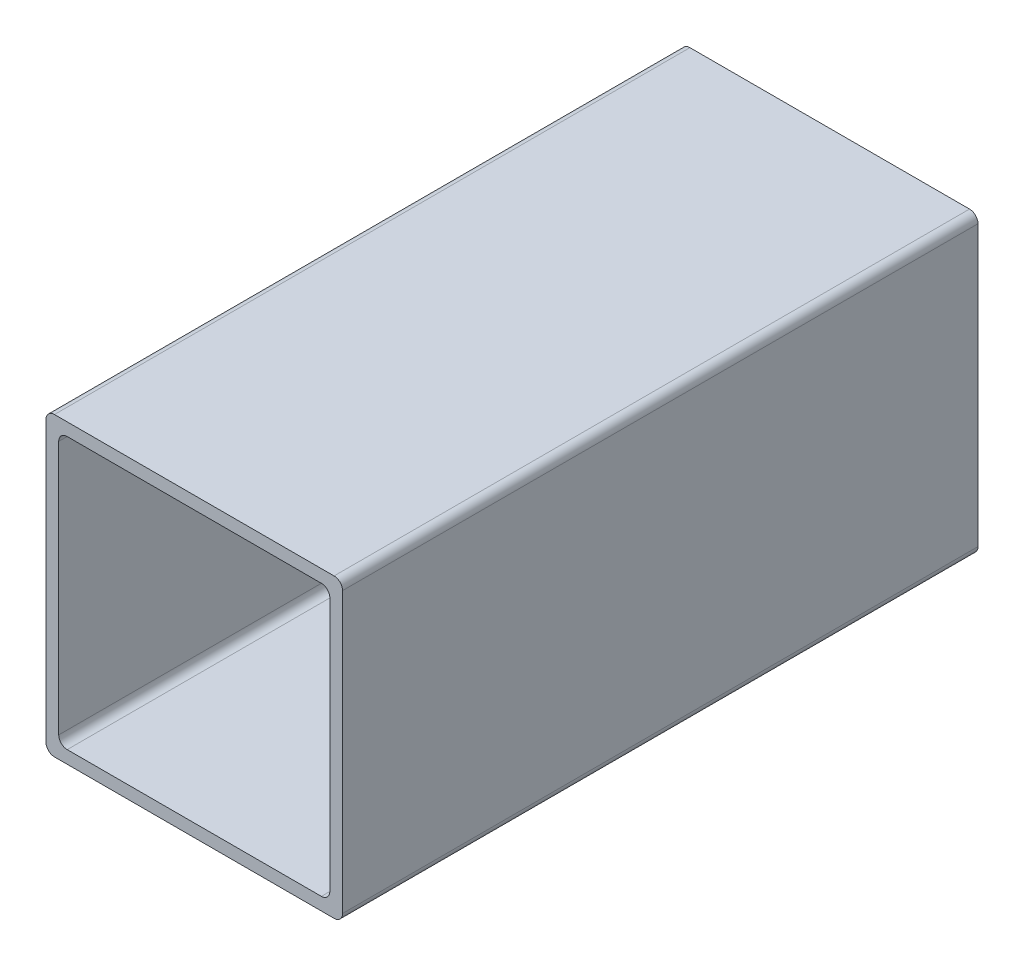
SolidWorks part; units mm, degrees
material "PMMA"
ref_plane "前视基准面" through (0, 0, 0) normal (0, 0, 1) x (1, 0, 0)
ref_plane "上视基准面" through (0, 0, 0) normal (0, 1, 0) x (1, 0, 0)
ref_plane "右视基准面" through (0, 0, 0) normal (1, 0, 0) x (0, 0, -1)
sketch "草图1" plane through (0, 0, 0) normal (0, 0, 1) x (1, 0, 0)
  line L1 (-35, 35) -> (35, 35)
  line L2 (-35, 35) -> (-35, -35)
  line L3 (-35, -35) -> (35, -35)
  line L4 (35, 35) -> (35, -35)
  line L5 (-35, 35) -> (35, -35) construction
  line L6 (-35, -35) -> (35, 35) construction
  line L7 (-32, 32) -> (32, 32)
  line L8 (-32, 32) -> (-32, -32)
  line L9 (-32, -32) -> (32, -32)
  line L10 (32, 32) -> (32, -32)
  line L11 (-32, 32) -> (32, -32) construction
  line L12 (-32, -32) -> (32, 32) construction
  point P0 (0, 0)
  point P6 (0, 0)
  point P11 (0, 35)
  dimension "D1" = 70
  dimension "D2" = 70
  dimension "D3" = 3
extrude "凸台-拉伸1" add sketch "草图1" along normal blind 150
fillet "圆角1" radius 2 8 edges at (35, -35, 75) (35, 35, 75) (-35, 35, 75) (-35, -35, 75) (32, -32, 75) (-32, -32, 75) (32, 32, 75) (-32, 32, 75)
